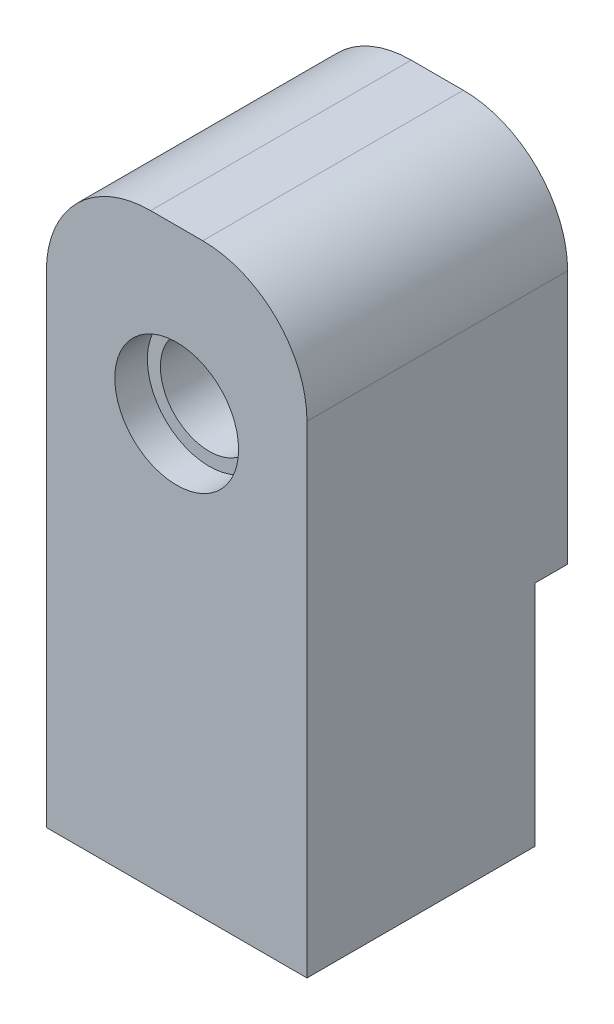
SolidWorks part; units mm, degrees
material "Plain Carbon Steel"
ref_plane "Front Plane" through (0, 0, 0) normal (0, 0, 1) x (1, 0, 0)
ref_plane "Top Plane" through (0, 0, 0) normal (0, 1, 0) x (1, 0, 0)
ref_plane "Right Plane" through (0, 0, 0) normal (1, 0, 0) x (0, 0, -1)
sketch "Sketch1" plane through (0, 0, 0) normal (0, 0, 1) x (1, 0, 0)
  line L1 (12.7, -28.575) -> (-12.7, -28.575)
  line L2 (12.7, -28.575) -> (12.7, 28.575)
  line L3 (12.7, 28.575) -> (-12.7, 28.575)
  line L4 (-12.7, -28.575) -> (-12.7, 28.575)
  line L5 (12.7, -28.575) -> (-12.7, 28.575) construction
  line L6 (12.7, 28.575) -> (-12.7, -28.575) construction
  point P0 (0, 0)
  dimension "D1" = 25.4
  dimension "D2" = 57.15
extrude "Boss-Extrude1" add sketch "Sketch1" against normal blind 25.4
sketch "Sketch2" plane through (0, 0, 0) normal (0, 0, 1) x (1, 0, 0)
  line L0 (12.7, 28.575) -> (-12.7, 28.575) construction
  circle A0 centre (0, 12.7) radius 6.0325
  dimension "D2" = 12.065
  dimension "D1" = 15.875
extrude "Cut-Extrude1" cut sketch "Sketch2" against normal blind 3.175
sketch "Sketch3" plane through (0, 0, -25.4) normal (0, 0, -1) x (-1, 0, 0)
  line L0 (-12.7, 28.575) -> (12.7, 28.575) construction
  circle A0 centre (0, 12.7) radius 4.7625
  dimension "D1" = 9.525
  dimension "D2" = 15.875
extrude "Cut-Extrude2" cut sketch "Sketch3" against normal up to next
sketch "Sketch4" plane through (0, 0, -25.4) normal (0, 0, -1) x (-1, 0, 0)
  line L0 (12.7, -28.575) -> (-12.7, -28.575) construction
  line L1 (12.7, -28.575) -> (-12.7, -28.575)
  line L2 (12.7, -28.575) -> (12.7, -6.35)
  line L3 (12.7, -6.35) -> (-12.7, -6.35)
  line L4 (-12.7, -28.575) -> (-12.7, -6.35)
  line L7 (-12.7, -28.575) -> (-12.7, 28.575) construction
  dimension "D3" = 22.225
extrude "Cut-Extrude4" cut sketch "Sketch4" against normal blind 3.175 contours L3 L4 L1 L2
sketch "Sketch6" plane through (0, -28.575, 0) normal (0, -1, 0) x (1, 0, 0)
  line L1 (-12.7, 0) -> (12.7, 0) construction
  line L5 (-12.7, -22.225) -> (-12.7, 0) construction
  circle A1 centre (0, -12.7) radius 6.35
  dimension "D1" = 12.7
  dimension "D2" = 12.7
  dimension "D3" = 12.7
extrude "Cut-Extrude5" cut sketch "Sketch6" against normal blind 30.1752
fillet "Fillet1" radius 10.16 2 edges at (-12.7, 28.575, -12.7) (12.7, 28.575, -12.7)
